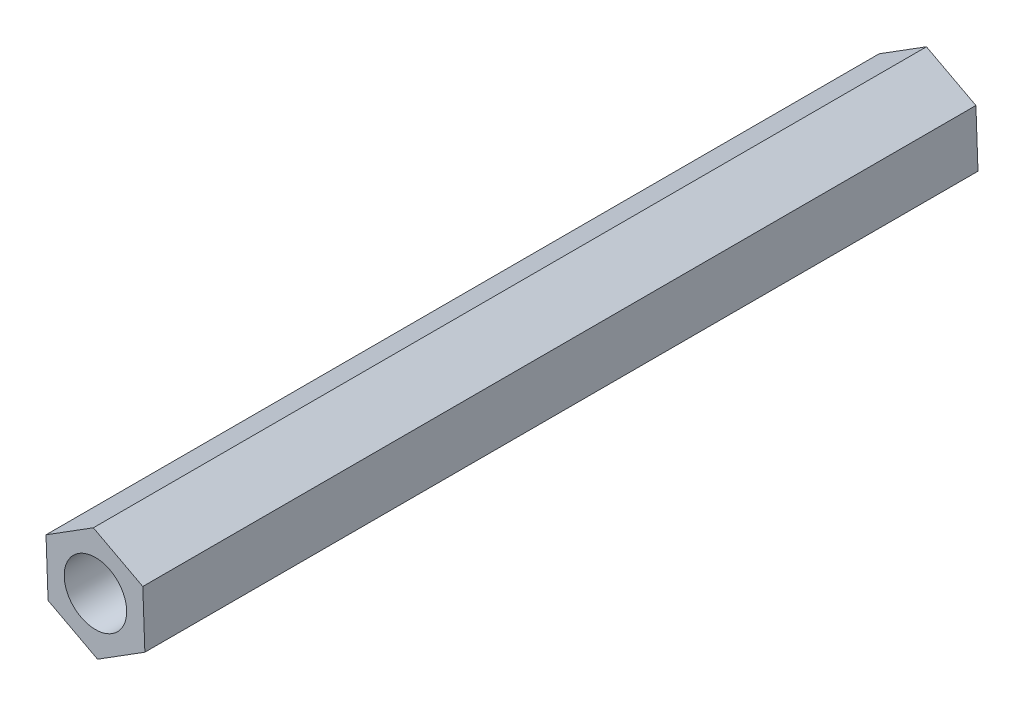
SolidWorks part; units mm, degrees
ref_plane "前视基准面" through (0, 0, 0) normal (0, 0, 1) x (1, 0, 0)
ref_plane "上视基准面" through (0, 0, 0) normal (0, 1, 0) x (1, 0, 0)
ref_plane "右视基准面" through (0, 0, 0) normal (1, 0, 0) x (0, 0, -1)
sketch "草图1" plane through (0, 0, 0) normal (0, 0, 1) x (1, 0, 0)
  line L1 (2.2732, 1.4283) -> (-0.1003, 2.6828)
  line L2 (-0.1003, 2.6828) -> (-2.3735, 1.2545)
  line L3 (-2.3735, 1.2545) -> (-2.2732, -1.4283)
  line L4 (-2.2732, -1.4283) -> (0.1003, -2.6828)
  line L5 (0.1003, -2.6828) -> (2.3735, -1.2545)
  line L6 (2.3735, -1.2545) -> (2.2732, 1.4283)
  circle A0 centre (0, 0) radius 2.325 construction
  circle A1 centre (0, 0) radius 1.5
extrude "凸台-拉伸1" add sketch "草图1" along normal blind 40
